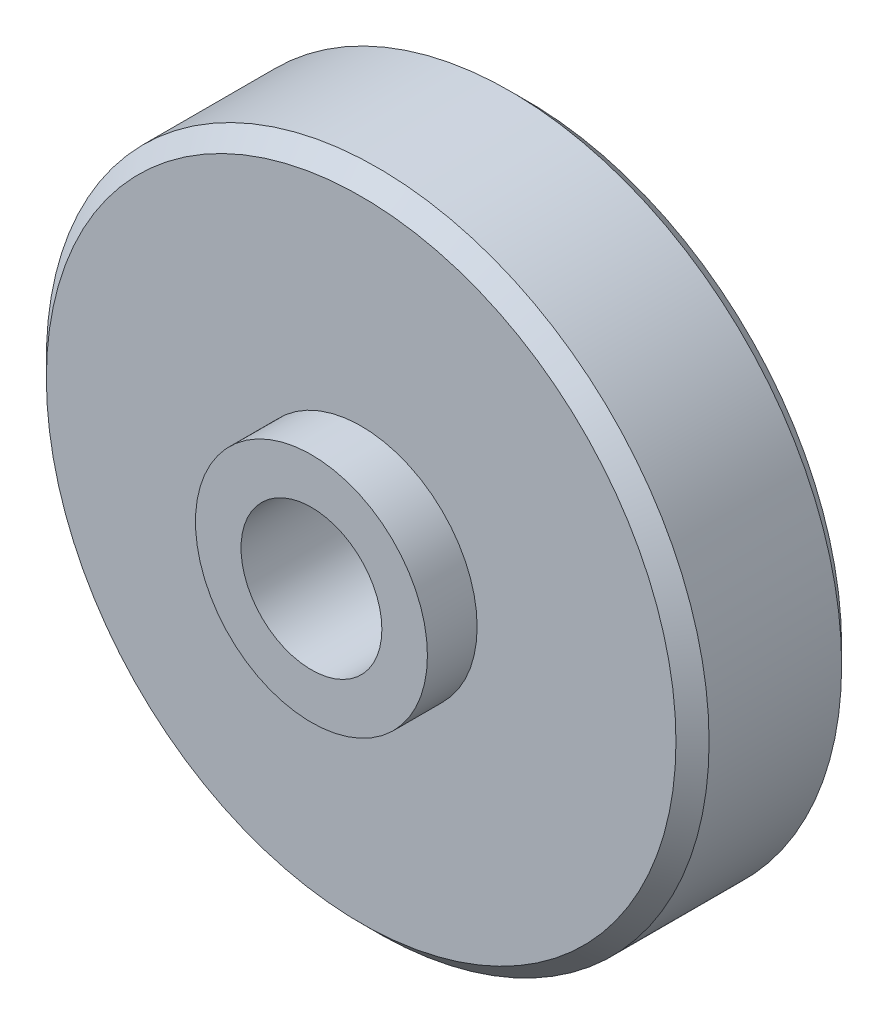
SolidWorks part; units mm, degrees
ref_plane "Plan de face" through (0, 0, 0) normal (0, 0, 1) x (1, 0, 0)
ref_plane "Plan de dessus" through (0, 0, 0) normal (0, 1, 0) x (1, 0, 0)
ref_plane "Plan de droite" through (0, 0, 0) normal (1, 0, 0) x (0, 0, -1)
sketch "Esquisse1" plane through (0, 0, 0) normal (0, 0, 1) x (1, 0, 0)
  circle A0 centre (0, 0) radius 20
  dimension "D1" = 40
extrude "Boss.-Extru.1" add sketch "Esquisse1" along normal blind 10
chamfer "Chanfrein1" distance 1 angle 45 2 edges at (20, 0, 0) (20, 0, 10)
sketch "Esquisse2" plane through (0, 0, 10) normal (0, 0, 1) x (1, 0, 0)
  circle A0 centre (0, 0) radius 7
  circle A1 centre (0, 0) radius 20 construction
  dimension "D1" = 13
extrude "Boss.-Extru.2" add sketch "Esquisse2" along normal blind 3
sketch "Esquisse3" plane through (0, 0, 13) normal (0, 0, 1) x (1, 0, 0)
  circle A0 centre (0, 0) radius 4
  dimension "D1" = 8
hole_wizard "Trou taraudé M101" positions "Esquisse5" profile "Esquisse4" tap size "M10" standard "ISO" end condition through all
sketch "Esquisse5" plane through (0, 0, 13) normal (0, 0, 1) x (1, 0, 0)
  point P0 (0, 0)
cosmetic thread "Filetage de perçage1"
sketch "Esquisse4" plane through (0, 0, 13) normal (1, 0, 0) x (0, -1, 0)
  line L0 (0, 0) -> (0, 13)
  line L1 (0, 13) -> (4.25, 13)
  line L2 (4.25, 13) -> (4.25, 0)
  line L5 (4.25, 0) -> (0, 0)
  line L11 (0, -6.35) -> (0, 107.95) construction
  dimension "Diamètre du trou pour taraudage jusqu'au prochain" = 8.5
  dimension "Profondeur du trou pour taraudage jusqu'au prochain" = 13
